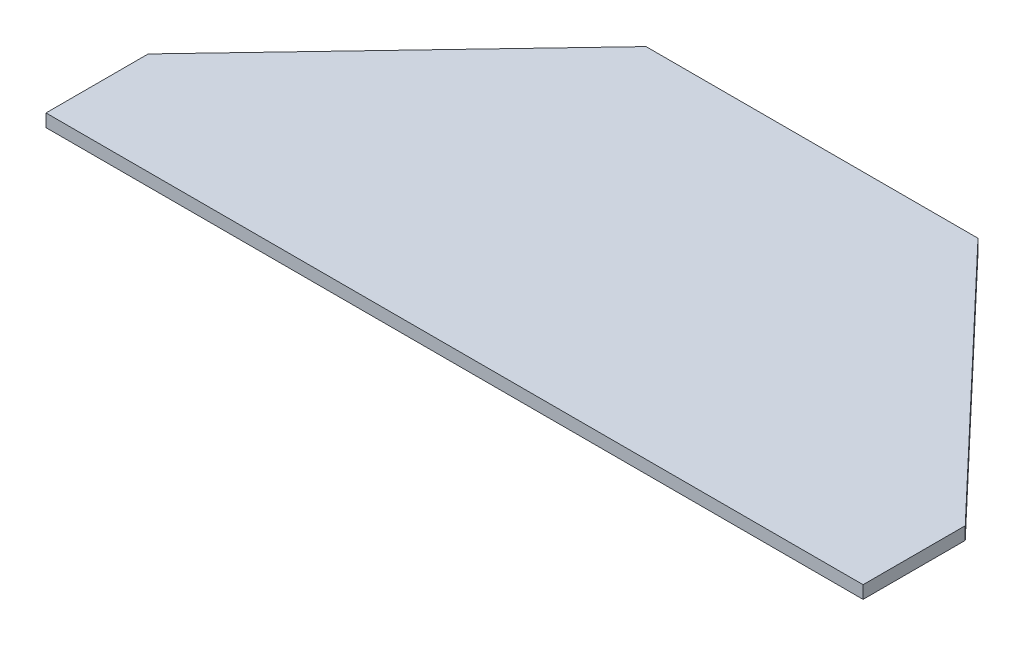
SolidWorks part; units mm, degrees
ref_plane "Front Plane" through (0, 0, 0) normal (0, 0, 1) x (1, 0, 0)
ref_plane "Top Plane" through (0, 0, 0) normal (0, 1, 0) x (1, 0, 0)
ref_plane "Right Plane" through (0, 0, 0) normal (1, 0, 0) x (0, 0, -1)
sketch "Sketch1" plane through (0, 0, 0) normal (0, 1, 0) x (1, 0, 0)
  line L0 (-203.2, 0) -> (203.2, 0)
  line L1 (203.2, 0) -> (203.2, 50.8)
  line L2 (203.2, 50.8) -> (82.55, 177.8)
  line L3 (82.55, 177.8) -> (-82.55, 177.8)
  line L4 (-82.55, 177.8) -> (-203.2, 50.8)
  line L5 (-203.2, 50.8) -> (-203.2, 0)
  point P5 (12.1412, 20.9425)
  point P8 (117.4665, 154.3394)
  point P9 (0, 0)
  point P10 (-86.6112, 146.05)
  point P12 (0, 177.8)
  dimension "D1" = 120.65
  dimension "D2" = 406.4
  dimension "D3" = 50.8
  dimension "D4" = 177.8
  dimension "D5" = 120.65
  dimension "D6" = 165.1
extrude "Boss-Extrude1" add sketch "Sketch1" along normal mid plane 6.35
ref_plane "Start of Actuator" through (0, 0, -50.8) normal (0, 0, -1) x (-1, 0, 0)
